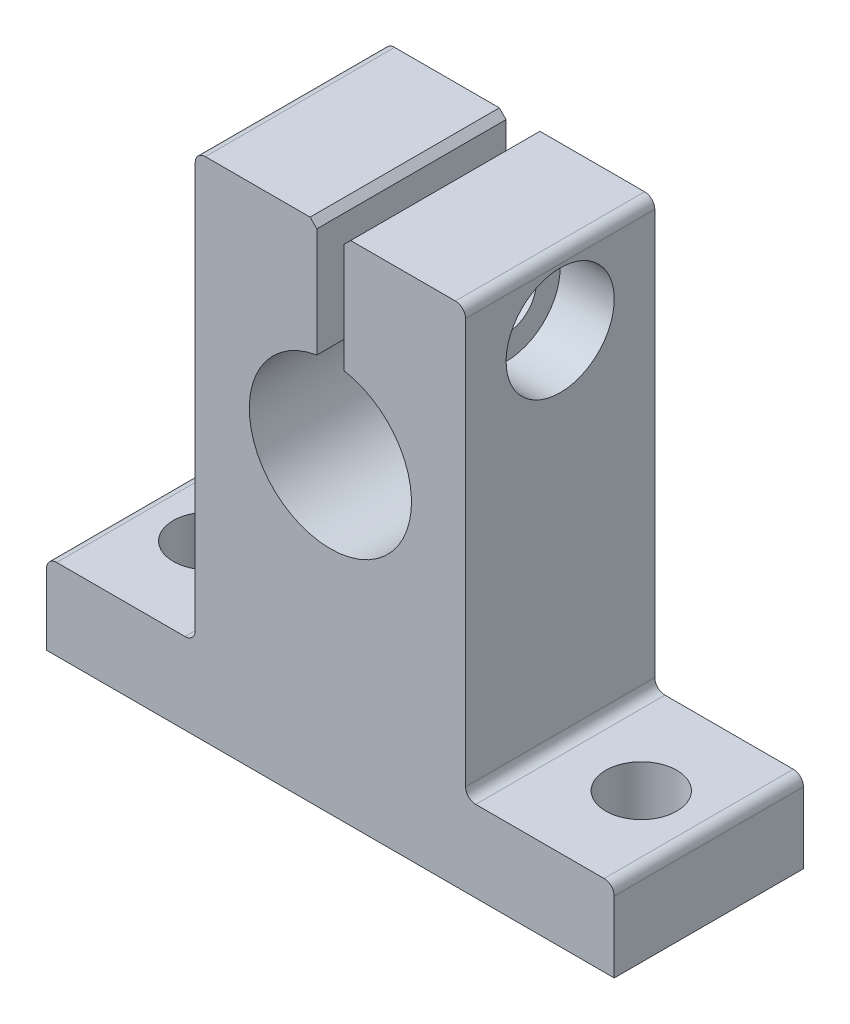
SolidWorks part; units mm, degrees
material "aluminio"
ref_plane "Alzado" through (0, 0, 0) normal (0, 0, 1) x (1, 0, 0)
ref_plane "Planta" through (0, 0, 0) normal (0, 1, 0) x (1, 0, 0)
ref_plane "Vista lateral" through (0, 0, 0) normal (1, 0, 0) x (0, 0, -1)
sketch "Croquis1" plane through (0, 0, 0) normal (0, 0, 1) x (1, 0, 0)
  line L0 (-21, 0) -> (21, 0)
  line L1 (21, 0) -> (21, 6)
  line L2 (21, 6) -> (10, 6)
  line L3 (10, 6) -> (10, 37.5)
  line L4 (10, 37.5) -> (-10, 37.5)
  line L5 (0, 37.5) -> (0, 0) construction
  line L6 (-1, 28.9161) -> (-1, 37.5)
  line L7 (1, 37.5) -> (1, 28.9161)
  line L10 (-10, 6) -> (-10, 37.5)
  line L11 (-21, 6) -> (-10, 6)
  line L12 (-21, 0) -> (-21, 6)
  arc A0 (-1, 28.9161) -> (1, 28.9161) centre (0, 23) ccw
  dimension "D3" = 12
  dimension "D1" = 37.5
  dimension "D2" = 21
  dimension "D4" = 10
  dimension "D5" = 23
  dimension "D6" = 6
  dimension "D7" = 1
extrude "Saliente-Extruir1" add sketch "Croquis1" along normal blind 14 contours A0 L5 L0 L1 L2 L3 L4 L7 | L5 A0 L6 L4 L10 L11 L12 L0
hole_wizard "Taladro roscado M43" positions "Croquis17" profile "Croquis16" tap size "M4" standard "ISO"
sketch "Croquis17" plane through (-1, 0, 0) normal (1, 0, 0) x (0, 0, -1)
  line L0 (-7, 37.5) -> (-7, 31.8242) construction
  line L1 (-14, 37.5) -> (0, 37.5) construction
  point P0 (-7, 32.5)
  dimension "D1" = 5
sketch "Croquis16" plane through (-1, 32.5, 7) normal (0, 1, 0) x (0, 0, -1)
  line L0 (0, 0) -> (0, 20)
  line L1 (0, 20) -> (1.65, 20)
  line L2 (1.65, 20) -> (1.65, 0)
  line L5 (1.65, 0) -> (0, 0)
  line L11 (0, -6.35) -> (0, 107.95) construction
  dimension "Diámetro de perforador para roscar hasta el siguiente" = 3.3
  dimension "Profundidad de perforador para roscar hasta el siguiente" = 20
cosmetic thread "Rosca de taladro6" parameters "D2"=4
sketch "Croquis4" plane through (0, 6, 0) normal (0, 1, 0) x (1, 0, 0)
  line L0 (-21, -7) -> (0, -7) construction
  line L1 (-21, -14) -> (-21, 0) construction
  line L2 (0, -7) -> (0, 0) construction
  circle A0 centre (-16, -7) radius 2.625
  circle A1 centre (16, -7) radius 2.625
  dimension "D1" = 5.25
  dimension "D2" = 16
extrude "Cortar-Extruir3" cut sketch "Croquis4" against normal up to next
fillet "Redondeo0,75mm" radius 0.75 6 edges at (-21, 6, 7) (21, 6, 7) (10, 37.5, 7) (-10, 37.5, 7) (10, 6, 7) (-10, 6, 7)
chamfer "Chaflán0,5mm" distance 0.5 angle 45 2 edges at (-1, 37.5, 7) (1, 37.5, 7)
sketch "Croquis24" plane through (10, 0, 0) normal (1, 0, 0) x (0, 0, -1)
  circle A0 centre (-7, 32.5) radius 2.25
  circle A1 centre (-7, 32.5) radius 1.65 construction
  dimension "D1" = 4.5
extrude "Cortar-Extruir5" cut sketch "Croquis24" against normal up to next
sketch "Croquis23" plane through (10, 0, 0) normal (-1, 0, 0) x (0, 0, 1)
  circle A0 centre (7, 32.5) radius 4
  dimension "D1" = 8
extrude "Cortar-Extruir4" cut sketch "Croquis23" along normal blind 4
